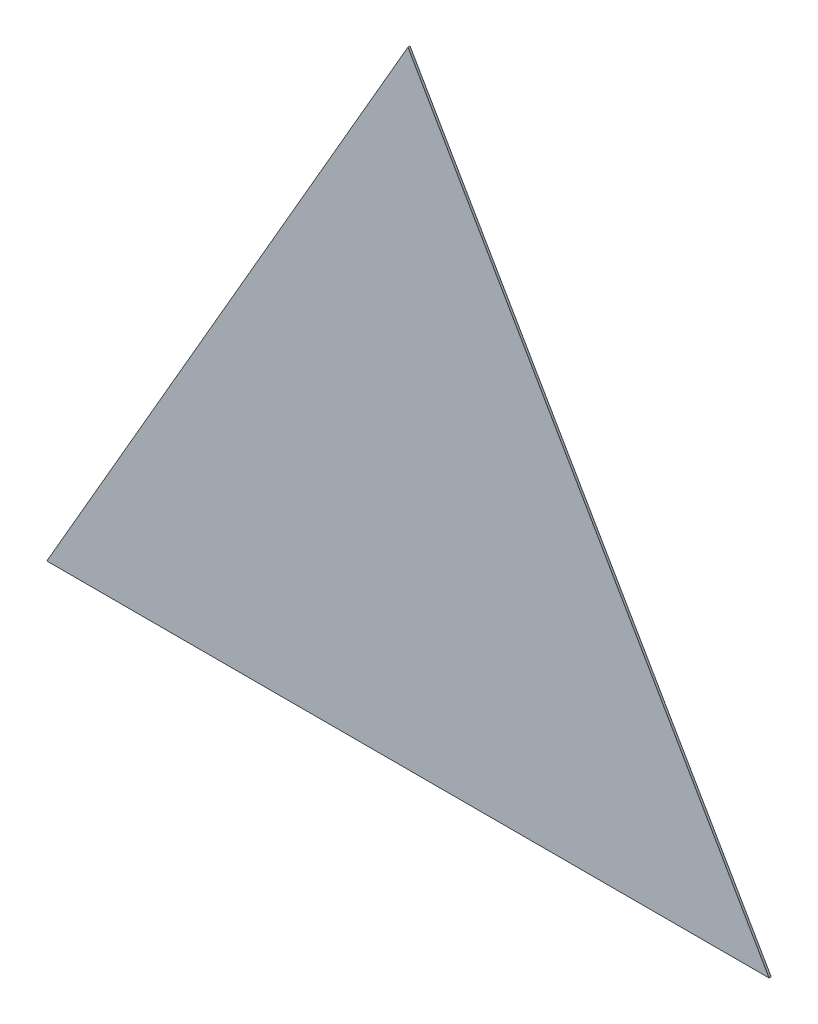
SolidWorks part; units mm, degrees
ref_plane "Спереди" through (0, 0, 0) normal (0, 0, 1) x (1, 0, 0)
ref_plane "Сверху" through (0, 0, 0) normal (0, 1, 0) x (1, 0, 0)
ref_plane "Справа" through (0, 0, 0) normal (1, 0, 0) x (0, 0, -1)
sketch "Эскиз1" plane through (0, 0, 0) normal (0, 0, 1) x (1, 0, 0)
  line L1 (0, 400) -> (-346.4102, -200)
  line L2 (-346.4102, -200) -> (346.4102, -200)
  line L3 (346.4102, -200) -> (0, 400)
  circle A0 centre (0, 0) radius 200 construction
extrude "Бобышка-Вытянуть1" add sketch "Эскиз1" along normal blind 2
